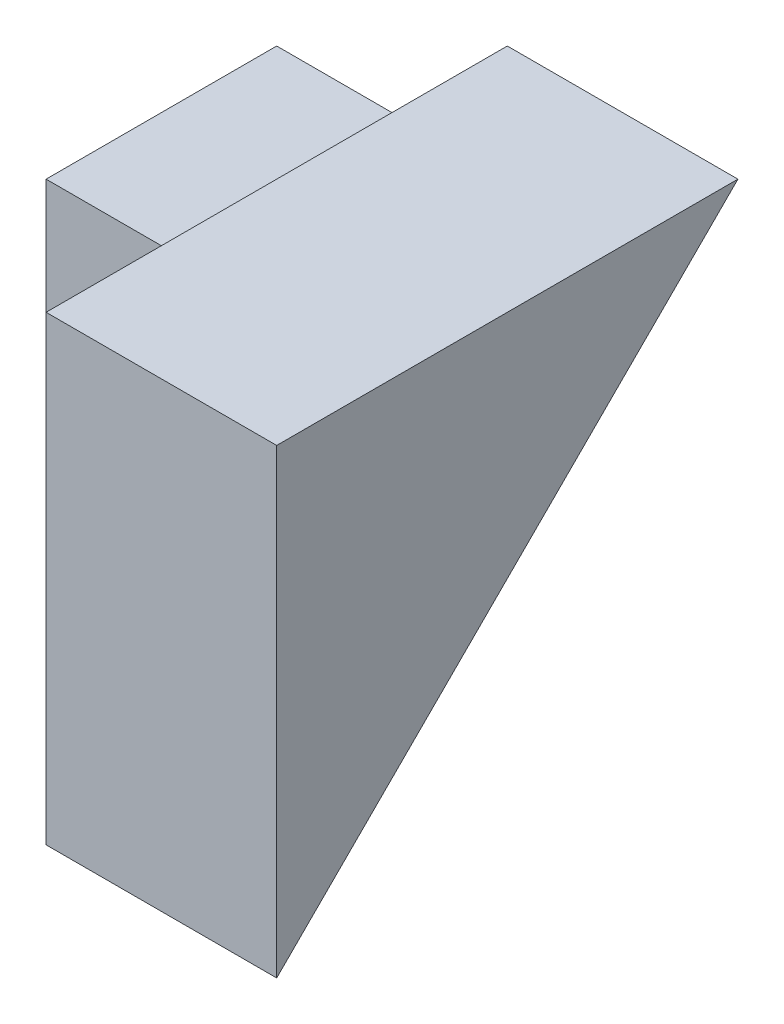
SolidWorks part; units mm, degrees
ref_plane "Front Plane" through (0, 0, 0) normal (0, 0, 1) x (1, 0, 0)
ref_plane "Top Plane" through (0, 0, 0) normal (0, 1, 0) x (1, 0, 0)
ref_plane "Right Plane" through (0, 0, 0) normal (1, 0, 0) x (0, 0, -1)
sketch "Sketch1" plane through (0, 0, 0) normal (1, 0, 0) x (0, 0, -1)
  line L1 (0, 0) -> (4, 0)
  line L2 (0, 0) -> (0, 4)
  line L3 (0, 4) -> (4, 4)
  line L4 (4, 0) -> (4, 4)
  dimension "D1" = 4
  dimension "D2" = 4
extrude "Boss-Extrude1" add sketch "Sketch1" along normal blind 2
sketch "Sketch2" plane through (0, 0, 0) normal (-1, 0, 0) x (0, 0, 1)
  line L1 (-4, 0) -> (-2, 0)
  line L2 (-4, 0) -> (-4, 3)
  line L3 (-4, 3) -> (-2, 3)
  line L4 (-2, 0) -> (-2, 3)
  dimension "D1" = 3
  dimension "D2" = 2
extrude "Boss-Extrude2" add sketch "Sketch2" along normal blind 2
sketch "Sketch3" plane through (2, 0, 0) normal (1, 0, 0) x (0, 0, -1)
  line L0 (4, 4) -> (0, 0)
  line L1 (0, 0) -> (0, 4)
  line L2 (0, 4) -> (4, 4)
  line M5 (0, 0) -> (4, 0)
  line M6 (4, 0) -> (4, 4)
extrude "Cut-Extrude1" cut sketch "Sketch3" against normal blind 2 contours L0 M6 M5
